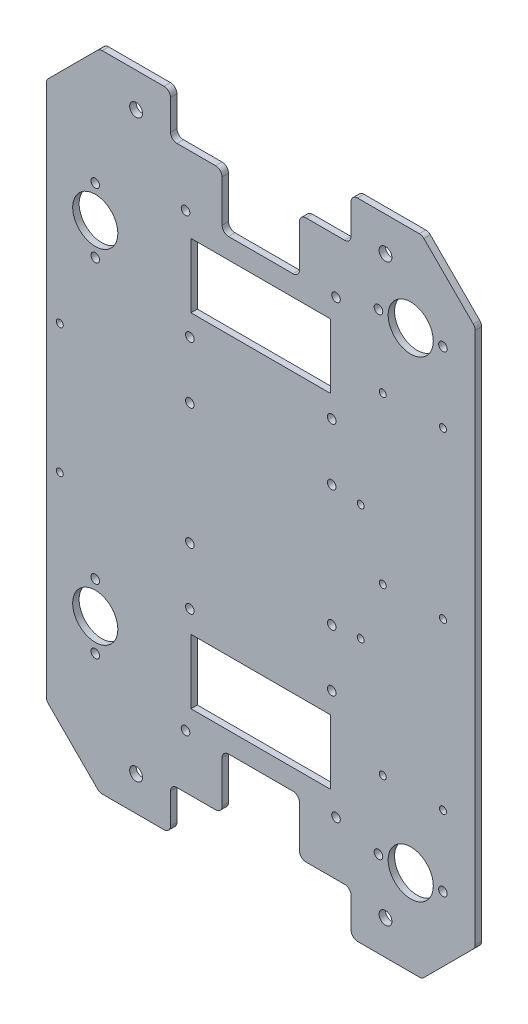
SolidWorks part; units mm, degrees
material "Alliage 1060"
ref_plane "Plan de dessus" through (0, 0, 0) normal (0, 0, 1) x (1, 0, 0)
ref_plane "Plan de droite" through (0, 0, 0) normal (0, 1, 0) x (1, 0, 0)
ref_plane "Plan de face" through (0, 0, 0) normal (1, 0, 0) x (0, 0, -1)
sketch "Esquisse1" plane through (0, 0, 0) normal (0, 0, 1) x (1, 0, 0)
  line L0 (0, 0) -> (-150, 0)
  line L1 (-150, 0) -> (-174.7487, 24.7487)
  line L2 (-174.7487, 24.7487) -> (-174.7487, 274.7487)
  line L3 (-174.7487, 274.7487) -> (-150, 299.4975)
  line L4 (-150, 299.4975) -> (0, 299.4975)
  line L5 (0, 299.4975) -> (24.7487, 274.7487)
  line L6 (24.7487, 274.7487) -> (24.7487, 24.7487)
  line L7 (24.7487, 24.7487) -> (0, 0)
  dimension "D1" = 250
  dimension "D2" = 35
  dimension "D3" = 135
  dimension "D4" = 150
extrude "Base" add sketch "Esquisse1" along normal blind 3
sketch "Esquisse3" plane through (0, 0, 0) normal (0, 0, -1) x (-1, 0, 0)
  line L0 (117, 0) -> (117, 20)
  line L1 (150, 0) -> (0, 0) construction
  line L2 (117, 20) -> (93, 20)
  line L3 (93, 20) -> (93, 45.5)
  line L4 (93, 45.5) -> (57, 45.5)
  line L5 (57, 45.5) -> (57, 20)
  line L6 (57, 20) -> (33, 20)
  line L7 (33, 20) -> (33, 0)
  line L8 (-24.7487, 149.7487) -> (174.7487, 149.7487) construction
  line L9 (-24.7487, 24.7487) -> (-24.7487, 274.7487) construction
  line L10 (174.7487, 274.7487) -> (174.7487, 24.7487) construction
  line L11 (33, 0) -> (117, 0)
  line L12 (33, 299.4975) -> (117, 299.4975)
  line L13 (117, 299.4975) -> (117, 279.4975)
  line L14 (117, 279.4975) -> (93, 279.4975)
  line L15 (93, 279.4975) -> (93, 253.9975)
  line L16 (93, 253.9975) -> (57, 253.9975)
  line L17 (57, 253.9975) -> (57, 279.4975)
  line L18 (57, 279.4975) -> (33, 279.4975)
  line L19 (33, 279.4975) -> (33, 299.4975)
  line L20 (75, 45.5) -> (75, -49954.5) construction
  line L21 (0, 299.4975) -> (150, 299.4975) construction
  line L22 (42.5, 244.4975) -> (107.5, 244.4975)
  line L23 (42.5, 244.4975) -> (42.5, 214.4975)
  line L24 (42.5, 214.4975) -> (107.5, 214.4975)
  line L25 (107.5, 244.4975) -> (107.5, 214.4975)
  line L26 (107.5, 55) -> (107.5, 85)
  line L27 (42.5, 85) -> (107.5, 85)
  line L28 (42.5, 55) -> (107.5, 55)
  line L29 (42.5, 55) -> (42.5, 85)
  circle A0 centre (40, 45) radius 2
  circle A1 centre (110, 45) radius 2
  circle A2 centre (110, 254.4975) radius 2
  circle A3 centre (40, 254.4975) radius 2
  point P4 (75, 45.5)
  point P11 (75, 0)
  point P40 (75, 244.4975)
  dimension "D7" = 4
  dimension "D5" = 25
  dimension "D1" = 20
  dimension "D2" = 24
  dimension "D3" = 36
  dimension "D4" = 25.5
  dimension "D6" = 7
  dimension "D8" = 55
  dimension "D9" = 30
  dimension "D10" = 65
extrude "Enlèv. mat.-Extru.1" cut sketch "Esquisse3" against normal through all
fillet "Congé1" radius 3 24 edges at (-174.7487, 24.7487, 1.5) (24.7487, 24.7487, 1.5) (0, 0, 1.5) (-117, 20, 1.5) (-93, 45.5, 1.5) (-93, 20, 1.5) (-150, 0, 1.5) (-117, 0, 1.5) (-57, 45.5, 1.5) (-33, 20, 1.5) (-57, 20, 1.5) (-33, 0, 1.5) (24.7487, 274.7487, 1.5) (-117, 279.4975, 1.5) (-93, 253.9975, 1.5) (-174.7487, 274.7487, 1.5) (-150, 299.4975, 1.5) (-117, 299.4975, 1.5) (-93, 279.4975, 1.5) (-57, 253.9975, 1.5) (-33, 279.4975, 1.5) (-57, 279.4975, 1.5) (-33, 299.4975, 1.5) (0, 299.4975, 1.5)
sketch "Esquisse6" plane through (0, 0, 3) normal (0, 0, 1) x (1, 0, 0)
  line L0 (24.7487, 25.9914) -> (24.7487, 273.5061) construction
  line L1 (-117, 3) -> (-117, 17) construction
  line L2 (-75, 231.5685) -> (-75, -49768.4315) construction
  line L3 (-30, 0) -> (-1.2426, 0) construction
  line L4 (-42.5, 214.4975) -> (-107.5, 214.4975) construction
  line L5 (-203.2843, 149.7487) -> (49796.7157, 149.7487) construction
  line L6 (-174.7487, 273.5061) -> (-174.7487, 25.9914) construction
  line L11 (-152, 85) -> (-152, 70) construction
  line L13 (-152, 70) -> (-152, 55) construction
  line L15 (-148.7574, 0) -> (-120, 0) construction
  circle A25 centre (-152, 55) radius 2
  circle A26 centre (-152, 85) radius 2
  circle A27 centre (-152, 70) radius 10.5
  circle A38 centre (-5.2513, 40) radius 10.5
  circle A39 centre (-20.2513, 40) radius 2
  circle A40 centre (9.7487, 40) radius 2
  point P15 (-75, 214.4975)
  point P20 (-174.7487, 149.7487)
  dimension "D2" = 4
  dimension "D3" = 15
  dimension "D4" = 21
  dimension "D5" = 4
  dimension "D7" = 4
  dimension "D8" = 15
  dimension "D9" = 35
  dimension "D10" = 30
  dimension "D6" = 15
  dimension "D11" = 40
  dimension "D13" = 21
  dimension "D14" = 30
  dimension "D15" = 70
extrude "Perçage pour billes" cut sketch "Esquisse6" against normal up to next (3 mm away)
sketch "Esquisse11" plane through (-174.7487, 0, 0) normal (-1, 0, 0) x (0, 0, 1)
  line L0 (0, 149.7487) -> (3, 149.7487) construction
  line L1 (0, 273.5061) -> (0, 25.9914) construction
  line L2 (3, 273.5061) -> (3, 25.9914) construction
ref_plane "Plan1" through (0, 149.7487, 0) normal (0, 1, 0) x (1, 0, 0)
sketch "Esquisse8" plane through (0, 0, 3) normal (0, 0, 1) x (1, 0, 0)
  line L0 (-75, 253.9975) -> (-75, 85) construction
  line L1 (-60, 253.9975) -> (-90, 253.9975) construction
  line L2 (-107.5, 85) -> (-42.5, 85) construction
  line L3 (-120, 299.4975) -> (-148.7574, 299.4975) construction
  line L4 (-117, 282.4975) -> (-117, 296.4975) construction
  line L5 (-148.7574, 0) -> (-120, 0) construction
  line L6 (-117, 3) -> (-117, 17) construction
  circle A0 centre (-133, 16) radius 3
  circle A1 centre (-133, 283.4975) radius 3
  circle A2 centre (-17, 283.4975) radius 3
  circle A3 centre (-17, 16) radius 3
  dimension "D1" = 16
  dimension "D2" = 16
  dimension "D3" = 6
  dimension "D4" = 16
  dimension "D5" = 16
  dimension "D6" = 6
extrude "Perçage pour profilé" cut sketch "Esquisse8" against normal up to next
sketch "Esquisse10" plane through (0, 0, 3) normal (0, 0, 1) x (1, 0, 0)
  line L0 (-174.7487, 273.5061) -> (-174.7487, 25.9914) construction
  line L2 (-42.5, 214.4975) -> (-107.5, 214.4975) construction
  line L3 (-75, 214.4975) -> (-75, 85) construction
  line L4 (-107.5, 85) -> (-42.5, 85) construction
  line L5 (-174.7487, 149.7487) -> (24.7487, 149.7487) construction
  line L6 (24.7487, 25.9914) -> (24.7487, 273.5061) construction
  circle A0 centre (-108, 204.4975) radius 2
  circle A1 centre (-108, 177.9975) radius 2
  circle A2 centre (-42, 177.9975) radius 2
  circle A3 centre (-42, 204.4975) radius 2
  circle A4 centre (-42, 121.5) radius 2
  circle A5 centre (-42, 95) radius 2
  circle A6 centre (-108, 121.5) radius 2
  circle A7 centre (-108, 95) radius 2
  dimension "D1" = 26.5
  dimension "D2" = 33
  dimension "D3" = 4
  dimension "D4" = 4
  dimension "D5" = 10
extrude "Enlèv. mat.-Extru.3" cut sketch "Esquisse10" against normal through all
mirror "Symétrie2" about plane through (0, 149.7487, 0) normal (0, 1, 0) of "Perçage pour billes"
sketch "Esquisse12" plane through (0, 0, 0) normal (0, 0, -1) x (-1, 0, 0)
  line L0 (-24.7487, 25.9914) -> (-24.7487, 273.5061) construction
  circle A0 centre (-9.7487, 72.7487) radius 1.625
  circle A1 centre (-9.7487, 149.7487) radius 1.625
  circle A2 centre (-9.7487, 226.7487) radius 1.625
  circle A3 centre (18.2513, 226.7487) radius 1.625
  circle A4 centre (18.2513, 149.7487) radius 1.625
  circle A5 centre (18.2513, 72.7487) radius 1.625
  point P15 (-24.7487, 149.7487)
  dimension "D1" = 3.25
  dimension "D2" = 3.25
  dimension "D3" = 3.25
  dimension "D4" = 3.25
  dimension "D5" = 3.25
  dimension "D6" = 3.25
  dimension "D7" = 28
  dimension "D8" = 28
  dimension "D9" = 28
  dimension "D10" = 15
  dimension "D11" = 77
  dimension "D12" = 77
extrude "Enlèv. mat.-Extru.4" cut sketch "Esquisse12" against normal through all
sketch "Esquisse13" plane through (0, 0, 0) normal (0, 0, -1) x (-1, 0, 0)
  line L0 (-24.7487, 25.9914) -> (-24.7487, 273.5061) construction
  line L1 (174.7487, 273.5061) -> (174.7487, 25.9914) construction
  line L2 (1.65, 149.7487) -> (-1.65, 149.7487) construction
  circle A0 centre (28.5013, 122.7487) radius 1.625
  circle A1 centre (28.5013, 176.7487) radius 1.625
  circle A2 centre (18.2513, 149.7487) radius 1.625 construction
  circle A3 centre (168.4987, 119.7487) radius 1.625
  circle A4 centre (168.4987, 179.7487) radius 1.625
  dimension "D1" = 3.25
  dimension "D2" = 3.25
  dimension "D4" = 27
  dimension "D6" = 3.25
  dimension "D7" = 3.25
  dimension "D3" = 54
  dimension "D5" = 53.25
  dimension "D8" = 60
  dimension "D9" = 6.25
  dimension "D10" = 30
extrude "Enlèv. mat.-Extru.5" cut sketch "Esquisse13" against normal through all
